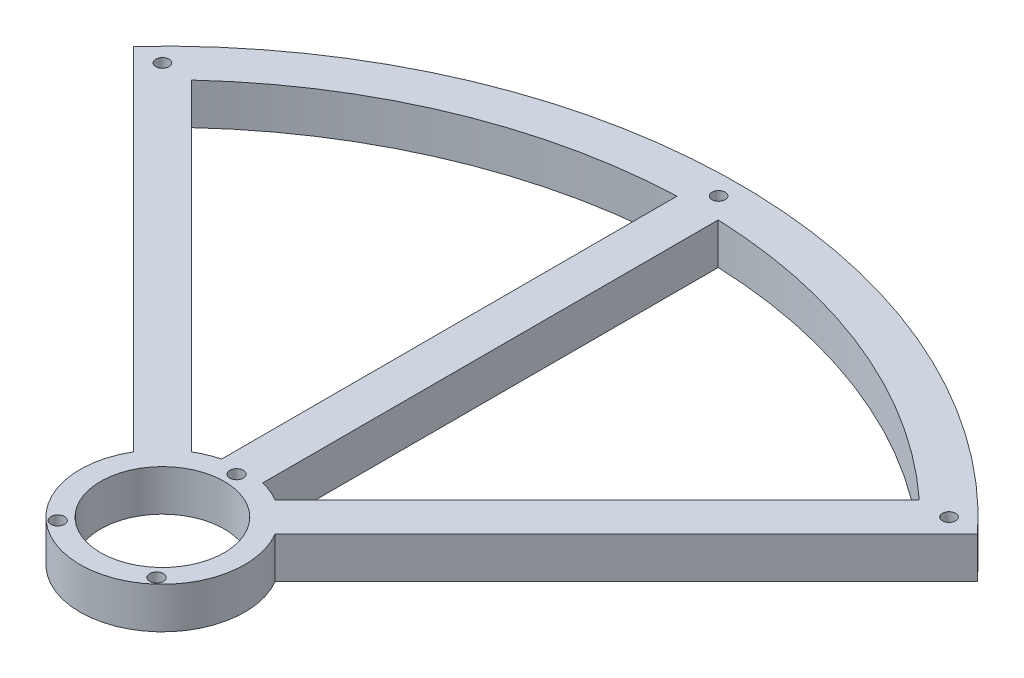
SolidWorks part; units mm, degrees
ref_plane "前基準面" through (0, 0, 0) normal (0, 0, 1) x (1, 0, 0)
ref_plane "上基準面" through (0, 0, 0) normal (0, 1, 0) x (1, 0, 0)
ref_plane "右基準面" through (0, 0, 0) normal (1, 0, 0) x (0, 0, -1)
sketch "草圖1" plane through (0, 0, 0) normal (0, 1, 0) x (1, 0, 0)
  line L0 (0, 41.9696) -> (0, -41.9696) construction
  line L1 (0, 0) -> (91.9239, 91.9239) construction
  line L2 (0, 0) -> (0, 130) construction
  line L3 (0, 0) -> (-91.9239, 91.9239) construction
  line L4 (17.2286, 10.1575) -> (95.4594, 88.3883)
  line L5 (17.2286, 10.1575) -> (10.1575, 17.2286) construction
  line L6 (95.4594, 88.3883) -> (88.3883, 95.4594) construction
  line L7 (10.1575, 17.2286) -> (88.3883, 95.4594)
  line L8 (17.2286, 10.1575) -> (88.3883, 95.4594) construction
  line L9 (95.4594, 88.3883) -> (10.1575, 17.2286) construction
  line L10 (-17.2286, 10.1575) -> (-10.1575, 17.2286) construction
  line L11 (-17.2286, 10.1575) -> (-95.4594, 88.3883)
  line L12 (-95.4594, 88.3883) -> (-10.1575, 17.2286) construction
  line L13 (-17.2286, 10.1575) -> (-88.3883, 95.4594) construction
  line L14 (-95.4594, 88.3883) -> (-88.3883, 95.4594) construction
  line L15 (-10.1575, 17.2286) -> (-88.3883, 95.4594)
  line L16 (-5, 130) -> (-5, 19.3649)
  line L17 (-5, 130) -> (5, 130)
  line L18 (-5, 19.3649) -> (5, 19.3649) construction
  line L19 (5, 130) -> (5, 19.3649)
  line L20 (-5, 130) -> (5, 19.3649) construction
  line L21 (-5, 19.3649) -> (5, 130) construction
  line L22 (-102.4673, 95.3963) -> (-95.4594, 88.3883)
  line L23 (102.4673, 95.3963) -> (95.4594, 88.3883)
  circle A0 centre (0, 0) radius 15
  circle A1 centre (0, 18) radius 1.65
  circle A2 centre (-12, -13.4164) radius 1.65
  circle A3 centre (12, -13.4164) radius 1.65
  arc A4 (-91.9239, 91.9239) -> (91.9239, 91.9239) centre (0, 0) cw
  circle A5 centre (0, 0) radius 20
  arc A6 (-102.4673, 95.3963) -> (102.4673, 95.3963) centre (0, 0) cw
  arc A7 (-98.9949, 98.9949) -> (98.9949, 98.9949) centre (0, 0) cw construction
  point P10 (0, 0)
  point P17 (52.8085, 52.8085)
  point P33 (0, 74.6825)
  dimension "D1" = 30
  dimension "D5" = 3.3
  dimension "D6" = 3.3
  dimension "D9" = 40
  dimension "D2" = 18
  dimension "D3" = 18
  dimension "D4" = 24
  dimension "D7" = 90
  dimension "D8" = 130
  dimension "D10" = 10
  dimension "D11" = 10
extrude "填料-伸長2" add sketch "草圖1" along normal blind 10
sketch "草圖2" plane through (0, 10, 0) normal (0, 1, 0) x (1, 0, 0)
  line L0 (0, 38.1871) -> (0, -50.097) construction
  line L1 (98.9949, 98.9949) -> (91.9239, 91.9239) construction
  line L2 (-102.4673, 95.3963) -> (-17.2286, 10.1575) construction
  line L3 (17.2286, 10.1575) -> (102.4673, 95.3963) construction
  line L4 (0, 0) -> (-98.9949, 98.9949) construction
  circle A0 centre (-95.4594, 95.4594) radius 1.6
  circle A1 centre (0, 135) radius 1.6
  arc A2 (98.9295, 91.8584) -> (-98.9295, 91.8584) centre (0, 0) ccw construction
  arc A3 (102.4673, 95.3963) -> (-102.4673, 95.3963) centre (0, 0) ccw construction
  arc A4 (88.3203, 95.3914) -> (5, 129.9038) centre (0, 0) ccw construction
  circle A5 centre (95.4594, 95.4594) radius 1.6
  point P8 (0, 0)
  point P20 (95.4594, 95.4594)
  dimension "D1" = 3.2
extrude "除料-伸長1" cut sketch "草圖2" against normal through all
